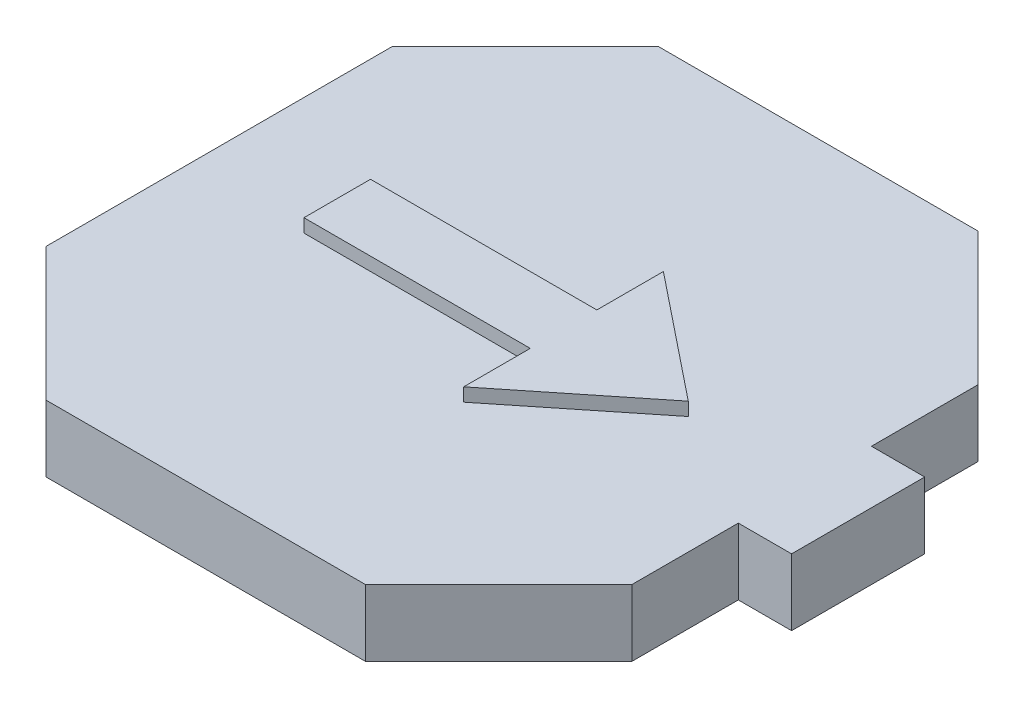
SolidWorks part; units mm, degrees
ref_plane "Plan de face" through (0, 0, 0) normal (0, 0, 1) x (1, 0, 0)
ref_plane "Plan de dessus" through (0, 0, 0) normal (0, 1, 0) x (1, 0, 0)
ref_plane "Plan de droite" through (0, 0, 0) normal (1, 0, 0) x (0, 0, -1)
sketch "Esquisse1" plane through (0, 0, 0) normal (0, 1, 0) x (1, 0, 0)
  line L0 (22, 13) -> (12.003, 23)
  line L1 (22, 13) -> (22, 5)
  line L2 (-22, -13) -> (-22, 13)
  line L3 (22, 5) -> (26, 5)
  line L4 (22, -5) -> (22, -13)
  line L5 (-22, -13) -> (22, 13) construction
  line L6 (-22, 13) -> (22, -13) construction
  line L7 (12.003, 23) -> (-12.003, 23)
  line L8 (-12.003, 23) -> (-22, 13)
  line L9 (-22, -13) -> (-12.003, -23)
  line L10 (-12.003, -23) -> (12.003, -23)
  line L11 (12.003, -23) -> (22, -13)
  line L12 (0, 23) -> (0, 0) construction
  line L13 (0, 0) -> (0, -23) construction
  line L14 (22, -5) -> (26, -5)
  line L15 (26, 5) -> (26, -5)
  point P1 (0, 0)
  dimension "D1" = 26
  dimension "D2" = 44
  dimension "D3" = 23
  dimension "D4" = 23
  dimension "D5" = 14.14
  dimension "D6" = 14.14
  dimension "D7" = 14.14
  dimension "D8" = 14.14
  dimension "D9" = 8
  dimension "D10" = 8
  dimension "D11" = 4
extrude "Boss.-Extru.1" add sketch "Esquisse1" along normal blind 5
sketch "Esquisse2" plane through (0, 5, 0) normal (0, 1, 0) x (1, 0, 0)
  line L0 (3.82, 2.5526) -> (3.82, 7.5526)
  line L1 (3.82, -2.4474) -> (-13.18, -2.4474)
  line L3 (3.82, 2.5526) -> (-13.18, 2.5526)
  line L4 (-13.18, -2.4474) -> (-13.18, 2.5526)
  line L7 (3.82, 7.5526) -> (13.1875, 0.0526)
  line L8 (13.1875, 0.0526) -> (3.82, -7.4474)
  line L9 (3.82, -7.4474) -> (3.82, -2.4474)
  line L10 (3.82, -2.4474) -> (4.0214, -2.4116)
  dimension "D1" = 5
  dimension "D2" = 5
  dimension "D3" = 17
  dimension "D4" = 17
  dimension "D5" = 12
  dimension "D6" = 12
  dimension "D7" = 5
extrude "Boss.-Extru.2" add sketch "Esquisse2" along normal blind 1
sketch "Esquisse3" plane through (0, 0, 0) normal (0, -1, 0) x (1, 0, 0)
  line L0 (-12.003, 23) -> (12.003, 23) construction
  line L1 (-16, 17) -> (-11, 17)
  line L2 (-16, 17) -> (-16, 12)
  line L3 (-16, 12) -> (-11, 12)
  line L4 (-11, 17) -> (-11, 12)
  line L5 (-16, 17) -> (-11, 12) construction
  line L6 (-16, 12) -> (-11, 17) construction
  line L8 (-22, -13) -> (-22, 13) construction
  line L9 (12.003, -23) -> (-12.003, -23) construction
  line L10 (-16, -17) -> (-11, -17)
  line L11 (-16, -17) -> (-16, -12)
  line L12 (-16, -12) -> (-11, -12)
  line L13 (-11, -17) -> (-11, -12)
  line L14 (-16, -17) -> (-11, -12) construction
  line L15 (-16, -12) -> (-11, -17) construction
  line L16 (12, -12) -> (17, -12)
  line L17 (12, -12) -> (12, -17)
  line L18 (12, -17) -> (17, -17)
  line L19 (17, -12) -> (17, -17)
  line L20 (12, -12) -> (17, -17) construction
  line L21 (12, -17) -> (17, -12) construction
  line L22 (11, 12) -> (16, 12)
  line L23 (11, 12) -> (11, 17)
  line L24 (11, 17) -> (16, 17)
  line L25 (16, 12) -> (16, 17)
  line L26 (11, 12) -> (16, 17) construction
  line L27 (11, 17) -> (16, 12) construction
  line L28 (22, -5) -> (22, -13) construction
  line L29 (22, 13) -> (22, 5) construction
  line L31 (-2.5, -2.5) -> (2.5, -2.5)
  line L32 (-2.5, -2.5) -> (-2.5, 2.5)
  line L33 (-2.5, 2.5) -> (2.5, 2.5)
  line L34 (2.5, -2.5) -> (2.5, 2.5)
  line L35 (-2.5, -2.5) -> (2.5, 2.5) construction
  line L36 (-2.5, 2.5) -> (2.5, -2.5) construction
  point P0 (-13.5, 14.5)
  point P9 (-13.5, -14.5)
  point P14 (14.5, -14.5)
  point P19 (13.5, 14.5)
  point P30 (0, 0)
  dimension "D1" = 5
  dimension "D2" = 5
  dimension "D3" = 6
  dimension "D4" = 6
  dimension "D5" = 5
  dimension "D6" = 5
  dimension "D7" = 5
  dimension "D8" = 5
  dimension "D9" = 5
  dimension "D10" = 5
  dimension "D11" = 6
  dimension "D12" = 6
  dimension "D13" = 6
  dimension "D14" = 5
  dimension "D15" = 6
  dimension "D16" = 6
  dimension "D17" = 5
  dimension "D18" = 5
  dimension "D19" = 20.5
  dimension "D20" = 20.5
  dimension "D21" = 19.5
  dimension "D22" = 19.5
extrude "Enlèv. mat.-Extru.1" cut sketch "Esquisse3" against normal blind 4.8
